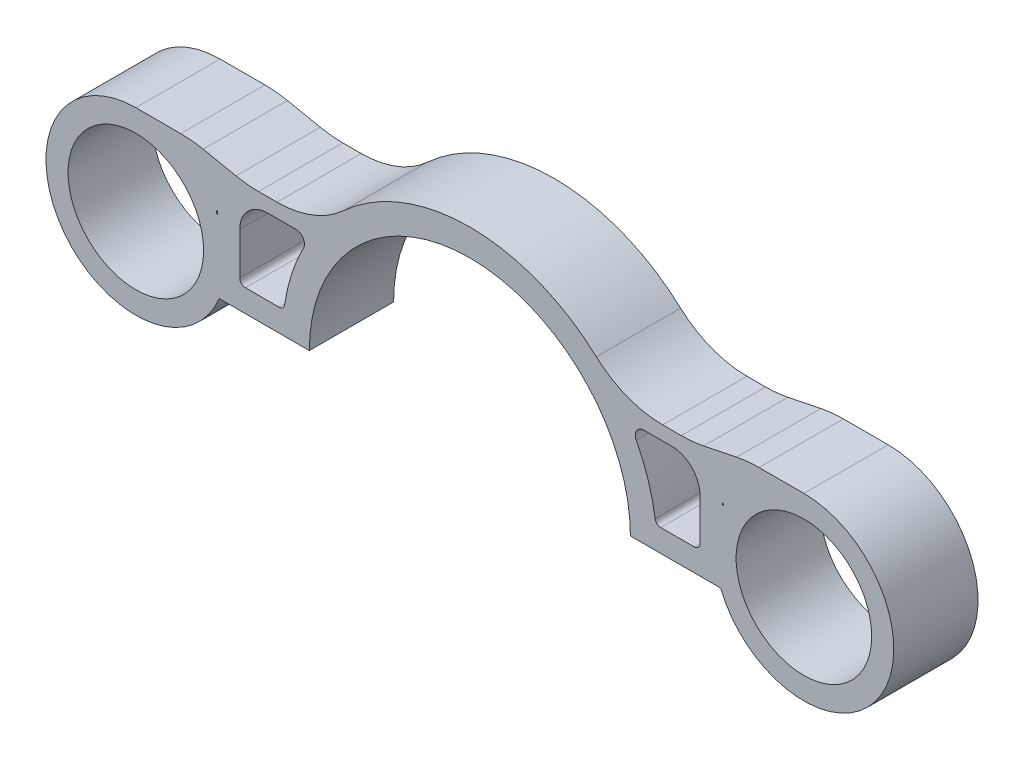
SolidWorks part; units mm, degrees
ref_plane "Front Plane" through (0, 0, 0) normal (0, 0, 1) x (1, 0, 0)
ref_plane "Top Plane" through (0, 0, 0) normal (0, 1, 0) x (1, 0, 0)
ref_plane "Right Plane" through (0, 0, 0) normal (1, 0, 0) x (0, 0, -1)
sketch "Sketch1" plane through (0, 0, 0) normal (0, 0, 1) x (1, 0, 0)
  line L0 (-66.675, 0) -> (-57.15, 0)
  line L1 (57.15, 0) -> (66.675, 0)
  circle A0 centre (0, 0) radius 57.15
  circle A1 centre (0, 0) radius 66.675
extrude "Boss-Extrude1" add sketch "Sketch1" along normal blind 30 contours L1 A1 L0 A0
sketch "Sketch2" plane through (0, 0, 30) normal (0, 0, 1) x (1, 0, 0)
  line L0 (-66.675, 0) -> (-57.15, 0) construction
  line L1 (-61.9125, 0) -> (-81.9125, 0)
  line L2 (-61.9125, 0) -> (-61.9125, 8)
  line L3 (-61.9125, 8) -> (-81.9125, 8)
  line L4 (-81.9125, 0) -> (-81.9125, 8)
  line L5 (57.15, 0) -> (66.675, 0) construction
  line L6 (61.9125, 0) -> (81.9125, 0)
  line L7 (61.9125, 0) -> (61.9125, 8)
  line L8 (61.9125, 8) -> (81.9125, 8)
  line L9 (81.9125, 0) -> (81.9125, 8)
  dimension "D1" = 20
  dimension "D2" = 8
  dimension "D3" = 20
  dimension "D4" = 8
extrude "Boss-Extrude2" add sketch "Sketch2" against normal blind 30
sketch "Sketch4" plane through (0, 0, 30) normal (0, 0, 1) x (1, 0, 0)
  line L0 (0, 66.675) -> (0, 0) construction
  line L1 (-81.9125, 0) -> (-89.9125, 0)
  line L2 (-81.9125, 0) -> (-81.9125, 35)
  line L3 (-81.9125, 35) -> (-89.9125, 35)
  line L4 (-89.9125, 0) -> (-89.9125, 35)
  line L5 (-89.9125, 35) -> (-42.5311, 35)
  line L6 (-89.9125, 35) -> (-89.9125, 40)
  line L7 (-89.9125, 40) -> (-42.5311, 40)
  line L8 (-42.5311, 35) -> (-42.5311, 40)
  line L9 (42.5311, 35) -> (42.5311, 40)
  line L10 (89.9125, 40) -> (42.5311, 40)
  line L11 (89.9125, 35) -> (89.9125, 40)
  line L12 (89.9125, 35) -> (42.5311, 35)
  line L13 (89.9125, 0) -> (89.9125, 35)
  line L14 (81.9125, 35) -> (89.9125, 35)
  line L15 (81.9125, 0) -> (81.9125, 35)
  line L16 (81.9125, 0) -> (89.9125, 0)
  arc A0 (66.1933, 8) -> (-66.1933, 8) centre (0, 0) ccw construction
  point P13 (0, 0)
  line M7 (81.9125, 0) -> (81.9125, 8)
  arc M9 (66.1933, 8) -> (-66.1933, 8) centre (0, 0) ccw
  line M11 (-81.9125, 8) -> (-81.9125, 0)
  dimension "D1" = 8
  dimension "D2" = 5
  dimension "D3" = 35
extrude "Boss-Extrude3" add sketch "Sketch4" against normal blind 30 contours L7 L6 L3 L5 M9 | L4 L1 L2 L3 M11 | L12 L11 L10 M9 | L16 L13 L12 L15 M7
fillet "Fillet2" radius 35 2 edges at (53.3437, 40, 15) (-53.3437, 40, 15)
fillet "Fillet3" radius 3 2 edges at (-56.7499, 35, 15) (56.7499, 35, 15)
sketch "Sketch5" plane through (0, 8, 0) normal (0, 1, 0) x (1, 0, 0)
  line L0 (-81.9125, -15) -> (81.9125, -15) construction
  line L1 (-81.9125, 0) -> (-81.9125, -30) construction
  line L2 (81.9125, 0) -> (81.9125, -30) construction
  line L3 (-74.0529, 0) -> (-74.0529, -30) construction
  line L4 (-66.1933, 0) -> (-81.9125, 0) construction
  line L5 (-66.1933, -30) -> (-81.9125, -30) construction
  line L6 (0, 0) -> (0, -33.9787) construction
  circle A0 centre (-74.0529, -15) radius 2.7781
  circle A1 centre (74.0529, -15) radius 2.7781
  point P15 (-74.0529, -15)
extrude "Cut-Extrude2" cut sketch "Sketch5" against normal through all
sketch "Sketch6" plane through (0, 0, 30) normal (0, 0, 1) x (1, 0, 0)
  line L0 (-89.9125, 0) -> (-57.15, 0) construction
  line L2 (-89.9125, 0) -> (-89.9125, 40) construction
  line L3 (-118.9125, 44) -> (-98.9125, 44)
  line L4 (-98.9125, 44) -> (-79.2812, 40)
  line L5 (-89.9125, 40) -> (-68.6499, 40) construction
  line L6 (-79.2812, 40) -> (-90.2792, 26.2876)
  line L7 (0, 0) -> (0, 57.15) construction
  line L8 (79.2812, 40) -> (90.2792, 26.2876)
  line L9 (98.9125, 44) -> (79.2812, 40)
  line L10 (118.9125, 44) -> (98.9125, 44)
  circle A0 centre (-118.9125, 12) radius 24.13
  circle A1 centre (-118.9125, 12) radius 32
  arc A2 (57.15, 0) -> (-57.15, 0) centre (0, 0) ccw construction
  circle A3 centre (118.9125, 12) radius 32
  circle A4 centre (118.9125, 12) radius 24.13
  line M3 (89.9125, 40) -> (68.6499, 40)
  line M7 (-68.6499, 40) -> (-89.9125, 40)
  line M8 (-89.9125, 40) -> (-89.9125, 0)
  line M9 (-89.9125, 0) -> (-57.15, 0)
  line M11 (57.15, 0) -> (89.9125, 0)
  line M12 (89.9125, 0) -> (89.9125, 40)
  dimension "D1" = 12
  dimension "D3" = 20
  dimension "D2" = 29
extrude "Boss-Extrude4" add sketch "Sketch6" against normal blind 30 contours A1 A0 M8 M9 | A1 L4 L3 M8 M7 | A3 L10 L9 M12 M3 | A3 A4 M12 M11
fillet "Fillet4" radius 40 4 edges at (79.2812, 40, 15) (98.9125, 44, 15) (-79.2812, 40, 15) (-98.9125, 44, 15)
fillet "Fillet5" radius 10 2 edges at (-81.9125, 35, 15) (81.9125, 35, 15)
fillet "Fillet6" radius 2 4 edges at (-66.1933, 8, 15) (-81.9125, 8, 15) (66.1933, 8, 15) (81.9125, 8, 15)
